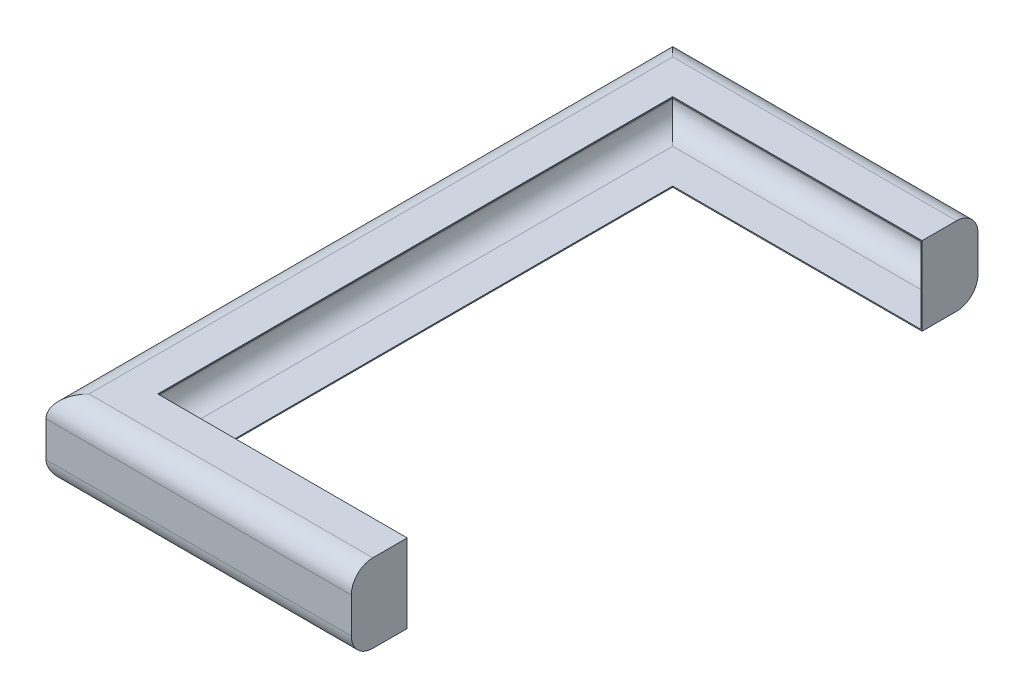
SolidWorks part; units mm, degrees
ref_plane "Front" through (0, 0, 0) normal (0, 0, 1) x (1, 0, 0)
ref_plane "Top" through (0, 0, 0) normal (0, 1, 0) x (1, 0, 0)
ref_plane "Right" through (0, 0, 0) normal (1, 0, 0) x (0, 0, -1)
sketch "Sketch1" plane through (0, 0, 0) normal (0, 1, 0) x (1, 0, 0)
  line L0 (368.3, 380.2126) -> (0, 380.2126)
  line L1 (0, 380.2126) -> (0, -380.2126)
  line L2 (0, -380.2126) -> (368.3, -380.2126)
  line L3 (368.3, -380.2126) -> (368.3, -462.7626)
  line L4 (368.3, -462.7626) -> (-82.55, -462.7626)
  line L5 (-82.55, -462.7626) -> (-82.55, 462.7626)
  line L6 (-82.55, 462.7626) -> (368.3, 462.7626)
  line L7 (368.3, 462.7626) -> (368.3, 380.2126)
  point P3 (0, 0)
  dimension "D1" = 82.55
  dimension "D2" = 82.55
  dimension "D3" = 760.4252
  dimension "D4" = 450.85
extrude "Boss-Extrude1" add sketch "Sketch1" along normal mid plane 115.8875
fillet "Fillet1" radius 31.75 6 edges at (142.875, -57.9437, 462.7626) (-82.55, -57.9437, 0) (142.875, -57.9437, -462.7626) (142.875, 57.9437, -462.7626) (-82.55, 57.9437, 0) (142.875, 57.9437, 462.7626)
shell "Shell1" thickness 1.5875
